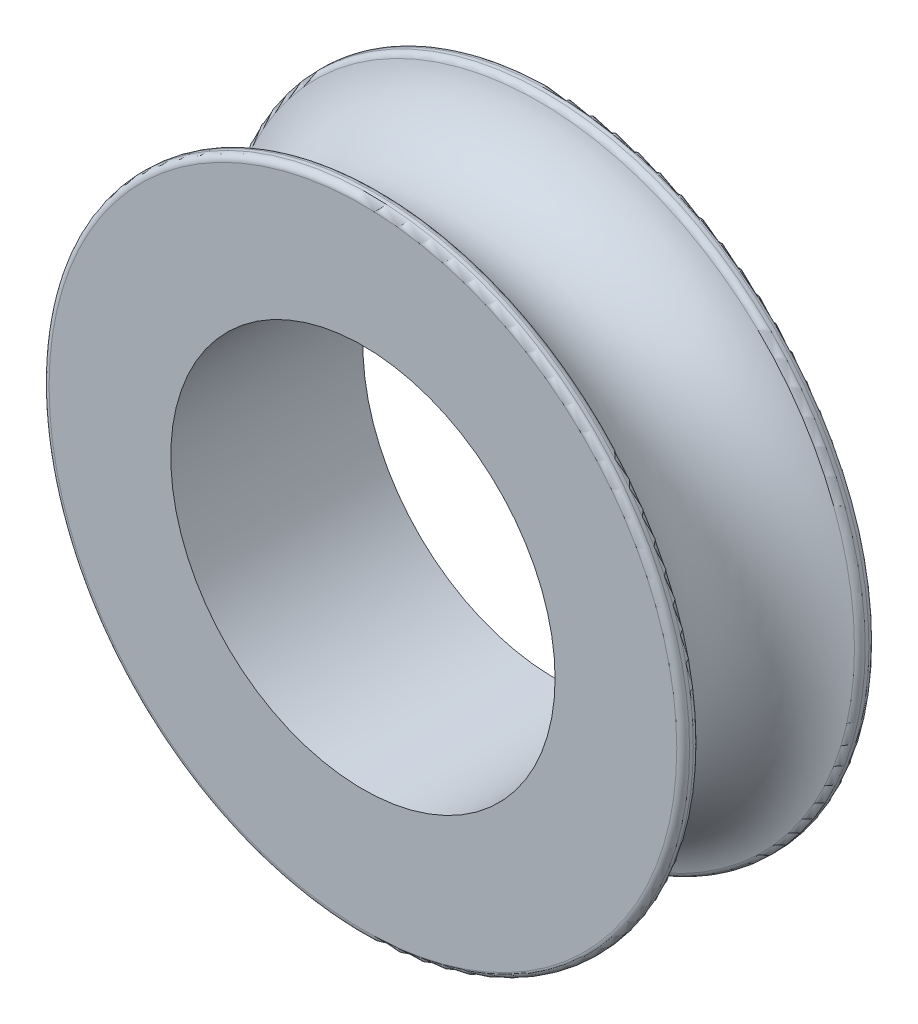
SolidWorks part; units mm, degrees
ref_plane "Plan de face" through (0, 0, 0) normal (0, 0, 1) x (1, 0, 0)
ref_plane "Plan de dessus" through (0, 0, 0) normal (0, 1, 0) x (1, 0, 0)
ref_plane "Plan de droite" through (0, 0, 0) normal (1, 0, 0) x (0, 0, -1)
sketch "Esquisse1" plane through (0, 0, 0) normal (1, 0, 0) x (0, 0, -1)
  line L0 (-1.5, 3) -> (-1.5, 5)
  line L1 (-1.5, 5) -> (-1.2649, 5)
  line L2 (1.5, 3) -> (1.5, 5)
  line L3 (1.5, 5) -> (1.2649, 5)
  line L4 (0, 0) -> (0, 6.7564) construction
  line L5 (0, 0) -> (4.2287, 0) construction
  line L6 (-1.5, 3) -> (1.5, 3)
  line L7 (1.5, 3) -> (1.5135, 2.9962)
  arc A0 (1.2649, 5) -> (-1.2649, 5) centre (0, 5.3) cw
  dimension "D2" = 1.3
  dimension "D1" = 10
  dimension "D3" = 2.3
revolve "Révolution1" add sketch "Esquisse1" angle 360 about L5
fillet "Congé2" radius 0.1 4 edges at (5, 0, 1.5) (5, 0, 1.2649) (5, 0, -1.2649) (5, 0, -1.5)
